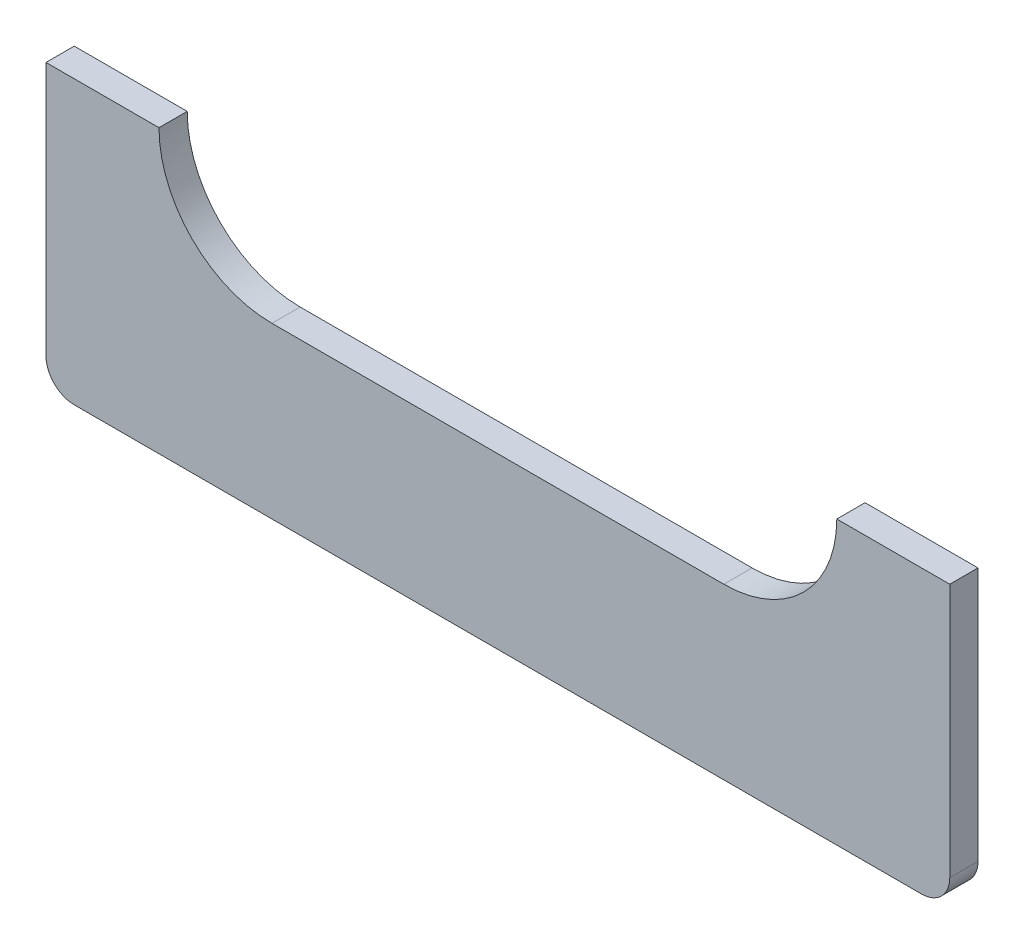
SolidWorks part; units mm, degrees
ref_plane "Front Plane" through (0, 0, 0) normal (0, 0, 1) x (1, 0, 0)
ref_plane "Top Plane" through (0, 0, 0) normal (0, 1, 0) x (1, 0, 0)
ref_plane "Right Plane" through (0, 0, 0) normal (1, 0, 0) x (0, 0, -1)
sketch "Sketch1" plane through (0, 0, 0) normal (0, 0, 1) x (1, 0, 0)
  line L0 (0, 15.9212) -> (0, -78.0293) construction
  line L1 (-101.6, 0) -> (-76.2, 0)
  line L2 (-101.6, 0) -> (-101.6, -63.5)
  line L3 (-101.6, -63.5) -> (101.6, -63.5)
  line L4 (101.6, 0) -> (101.6, -63.5)
  line L5 (-50.8, -25.4) -> (50.8, -25.4)
  line L6 (76.2, 0) -> (101.6, 0)
  arc A0 (-76.2, 0) -> (-50.8, -25.4) centre (-50.8, 0) ccw
  arc A1 (76.2, 0) -> (50.8, -25.4) centre (50.8, 0) cw
  dimension "D5" = 25.4
  dimension "D1" = 203.2
  dimension "D2" = 101.6
  dimension "D3" = 63.5
  dimension "D4" = 25.4
  dimension "D6" = 50.8
extrude "Extrude1" add sketch "Sketch1" along normal blind 6.35
fillet "Fillet1" radius 6.35 2 edges at (-101.6, -63.5, 3.175) (101.6, -63.5, 3.175)
